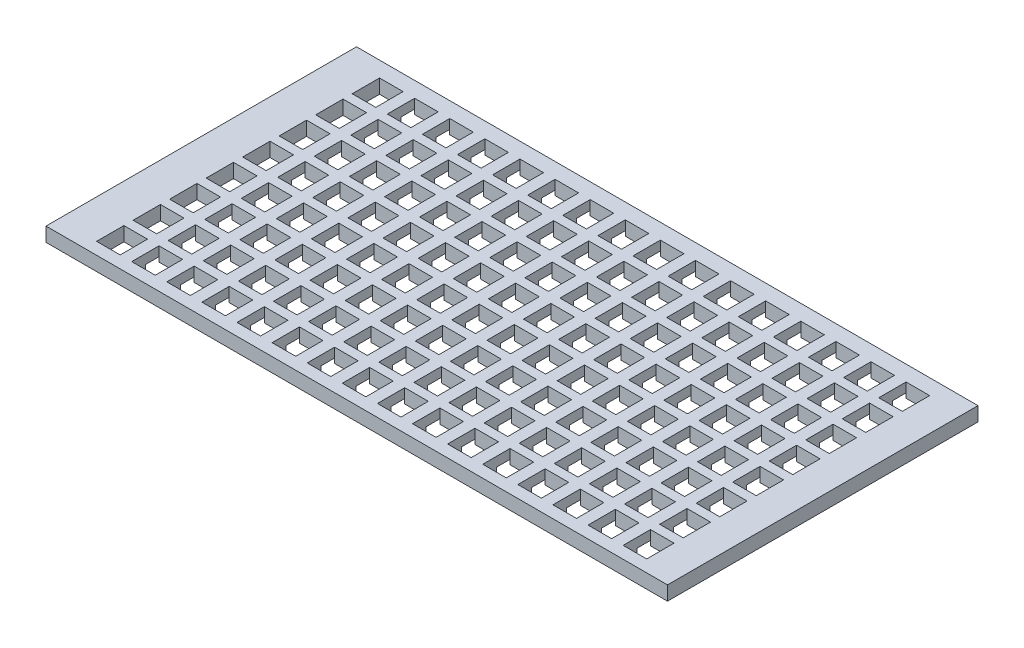
SolidWorks part; units mm, degrees
ref_plane "前视基准面" through (0, 0, 0) normal (0, 0, 1) x (1, 0, 0)
ref_plane "上视基准面" through (0, 0, 0) normal (0, 1, 0) x (1, 0, 0)
ref_plane "右视基准面" through (0, 0, 0) normal (1, 0, 0) x (0, 0, -1)
other "Configuration Table"
sketch "草图1" plane through (0, 0, 0) normal (0, 1, 0) x (1, 0, 0)
  line L1 (-65.95, 32.95) -> (65.95, 32.95)
  line L2 (-65.95, 32.95) -> (-65.95, -32.95)
  line L3 (-65.95, -32.95) -> (65.95, -32.95)
  line L4 (65.95, 32.95) -> (65.95, -32.95)
  line L5 (-65.95, 32.95) -> (65.95, -32.95) construction
  line L6 (-65.95, -32.95) -> (65.95, 32.95) construction
  point P0 (0, 0)
  dimension "D1" = 65.9
  dimension "D2" = 131.9
extrude "凸台-拉伸1" add sketch "草图1" along normal blind 3
sketch "草图2" plane through (0, 0, 0) normal (0, -1, 0) x (1, 0, 0)
  line L0 (-57.7744, 22.638) -> (-57.7744, 16.838)
  line L5 (-57.7744, 30.388) -> (-52.7744, 30.388)
  line L6 (-57.7744, 30.388) -> (-57.7744, 24.588)
  line L11 (-57.7744, 24.588) -> (-52.7744, 24.588)
  line L12 (-52.7744, 30.388) -> (-52.7744, 24.588)
  line L13 (-57.7744, 22.638) -> (-52.7744, 22.638)
  line L14 (-52.7744, 22.638) -> (-52.7744, 16.838)
  line L15 (-57.7744, 16.838) -> (-52.7744, 16.838)
  line L16 (-57.7744, 14.888) -> (-57.7744, 9.088)
  line L17 (-57.7744, 14.888) -> (-52.7744, 14.888)
  line L18 (-52.7744, 14.888) -> (-52.7744, 9.088)
  line L19 (-57.7744, 9.088) -> (-52.7744, 9.088)
  line L20 (-57.7744, 7.138) -> (-57.7744, 1.338)
  line L21 (-57.7744, 7.138) -> (-52.7744, 7.138)
  line L22 (-52.7744, 7.138) -> (-52.7744, 1.338)
  line L23 (-57.7744, 1.338) -> (-52.7744, 1.338)
  line L24 (-57.7744, -0.612) -> (-57.7744, -6.412)
  line L25 (-57.7744, -0.612) -> (-52.7744, -0.612)
  line L26 (-52.7744, -0.612) -> (-52.7744, -6.412)
  line L27 (-57.7744, -6.412) -> (-52.7744, -6.412)
  line L28 (-57.7744, -8.362) -> (-57.7744, -14.162)
  line L29 (-57.7744, -8.362) -> (-52.7744, -8.362)
  line L30 (-52.7744, -8.362) -> (-52.7744, -14.162)
  line L31 (-57.7744, -14.162) -> (-52.7744, -14.162)
  line L32 (-57.7744, -16.112) -> (-57.7744, -21.912)
  line L33 (-57.7744, -16.112) -> (-52.7744, -16.112)
  line L34 (-52.7744, -16.112) -> (-52.7744, -21.912)
  line L35 (-57.7744, -21.912) -> (-52.7744, -21.912)
  line L36 (-57.7744, -23.862) -> (-57.7744, -29.662)
  line L37 (-57.7744, -23.862) -> (-52.7744, -23.862)
  line L38 (-52.7744, -23.862) -> (-52.7744, -29.662)
  line L39 (-57.7744, -29.662) -> (-52.7744, -29.662)
  line L40 (-50.3244, 30.388) -> (-50.3244, 24.588)
  line L41 (-50.3244, 30.388) -> (-45.3244, 30.388)
  line L42 (-45.3244, 30.388) -> (-45.3244, 24.588)
  line L43 (-50.3244, 24.588) -> (-45.3244, 24.588)
  line L44 (-50.3244, 22.638) -> (-50.3244, 16.838)
  line L45 (-50.3244, 16.838) -> (-45.3244, 16.838)
  line L46 (-45.3244, 22.638) -> (-45.3244, 16.838)
  line L47 (-50.3244, 22.638) -> (-45.3244, 22.638)
  line L48 (-50.3244, 14.888) -> (-50.3244, 9.088)
  line L49 (-50.3244, 9.088) -> (-45.3244, 9.088)
  line L50 (-45.3244, 14.888) -> (-45.3244, 9.088)
  line L51 (-50.3244, 14.888) -> (-45.3244, 14.888)
  line L52 (-50.3244, 7.138) -> (-50.3244, 1.338)
  line L53 (-50.3244, 1.338) -> (-45.3244, 1.338)
  line L54 (-45.3244, 7.138) -> (-45.3244, 1.338)
  line L55 (-50.3244, 7.138) -> (-45.3244, 7.138)
  line L56 (-50.3244, -0.612) -> (-50.3244, -6.412)
  line L57 (-50.3244, -6.412) -> (-45.3244, -6.412)
  line L58 (-45.3244, -0.612) -> (-45.3244, -6.412)
  line L59 (-50.3244, -0.612) -> (-45.3244, -0.612)
  line L60 (-50.3244, -8.362) -> (-50.3244, -14.162)
  line L61 (-50.3244, -14.162) -> (-45.3244, -14.162)
  line L62 (-45.3244, -8.362) -> (-45.3244, -14.162)
  line L63 (-50.3244, -8.362) -> (-45.3244, -8.362)
  line L64 (-50.3244, -16.112) -> (-50.3244, -21.912)
  line L65 (-50.3244, -21.912) -> (-45.3244, -21.912)
  line L66 (-45.3244, -16.112) -> (-45.3244, -21.912)
  line L67 (-50.3244, -16.112) -> (-45.3244, -16.112)
  line L68 (-50.3244, -23.862) -> (-50.3244, -29.662)
  line L69 (-50.3244, -29.662) -> (-45.3244, -29.662)
  line L70 (-45.3244, -23.862) -> (-45.3244, -29.662)
  line L71 (-50.3244, -23.862) -> (-45.3244, -23.862)
  line L72 (-42.8744, 30.388) -> (-42.8744, 24.588)
  line L73 (-42.8744, 30.388) -> (-37.8744, 30.388)
  line L74 (-37.8744, 30.388) -> (-37.8744, 24.588)
  line L75 (-42.8744, 24.588) -> (-37.8744, 24.588)
  line L76 (-42.8744, 22.638) -> (-42.8744, 16.838)
  line L77 (-42.8744, 16.838) -> (-37.8744, 16.838)
  line L78 (-37.8744, 22.638) -> (-37.8744, 16.838)
  line L79 (-42.8744, 22.638) -> (-37.8744, 22.638)
  line L80 (-42.8744, 14.888) -> (-42.8744, 9.088)
  line L81 (-42.8744, 9.088) -> (-37.8744, 9.088)
  line L82 (-37.8744, 14.888) -> (-37.8744, 9.088)
  line L83 (-42.8744, 14.888) -> (-37.8744, 14.888)
  line L84 (-42.8744, 7.138) -> (-42.8744, 1.338)
  line L85 (-42.8744, 1.338) -> (-37.8744, 1.338)
  line L86 (-37.8744, 7.138) -> (-37.8744, 1.338)
  line L87 (-42.8744, 7.138) -> (-37.8744, 7.138)
  line L88 (-42.8744, -0.612) -> (-42.8744, -6.412)
  line L89 (-42.8744, -6.412) -> (-37.8744, -6.412)
  line L90 (-37.8744, -0.612) -> (-37.8744, -6.412)
  line L91 (-42.8744, -0.612) -> (-37.8744, -0.612)
  line L92 (-42.8744, -8.362) -> (-42.8744, -14.162)
  line L93 (-42.8744, -14.162) -> (-37.8744, -14.162)
  line L94 (-37.8744, -8.362) -> (-37.8744, -14.162)
  line L95 (-42.8744, -8.362) -> (-37.8744, -8.362)
  line L96 (-42.8744, -16.112) -> (-42.8744, -21.912)
  line L97 (-42.8744, -21.912) -> (-37.8744, -21.912)
  line L98 (-37.8744, -16.112) -> (-37.8744, -21.912)
  line L99 (-42.8744, -16.112) -> (-37.8744, -16.112)
  line L100 (-42.8744, -23.862) -> (-42.8744, -29.662)
  line L101 (-42.8744, -29.662) -> (-37.8744, -29.662)
  line L102 (-37.8744, -23.862) -> (-37.8744, -29.662)
  line L103 (-42.8744, -23.862) -> (-37.8744, -23.862)
  line L104 (-35.4244, 30.388) -> (-35.4244, 24.588)
  line L105 (-35.4244, 30.388) -> (-30.4244, 30.388)
  line L106 (-30.4244, 30.388) -> (-30.4244, 24.588)
  line L107 (-35.4244, 24.588) -> (-30.4244, 24.588)
  line L108 (-35.4244, 22.638) -> (-35.4244, 16.838)
  line L109 (-35.4244, 16.838) -> (-30.4244, 16.838)
  line L110 (-30.4244, 22.638) -> (-30.4244, 16.838)
  line L111 (-35.4244, 22.638) -> (-30.4244, 22.638)
  line L112 (-35.4244, 14.888) -> (-35.4244, 9.088)
  line L113 (-35.4244, 9.088) -> (-30.4244, 9.088)
  line L114 (-30.4244, 14.888) -> (-30.4244, 9.088)
  line L115 (-35.4244, 14.888) -> (-30.4244, 14.888)
  line L116 (-35.4244, 7.138) -> (-35.4244, 1.338)
  line L117 (-35.4244, 1.338) -> (-30.4244, 1.338)
  line L118 (-30.4244, 7.138) -> (-30.4244, 1.338)
  line L119 (-35.4244, 7.138) -> (-30.4244, 7.138)
  line L120 (-35.4244, -0.612) -> (-35.4244, -6.412)
  line L121 (-35.4244, -6.412) -> (-30.4244, -6.412)
  line L122 (-30.4244, -0.612) -> (-30.4244, -6.412)
  line L123 (-35.4244, -0.612) -> (-30.4244, -0.612)
  line L124 (-35.4244, -8.362) -> (-35.4244, -14.162)
  line L125 (-35.4244, -14.162) -> (-30.4244, -14.162)
  line L126 (-30.4244, -8.362) -> (-30.4244, -14.162)
  line L127 (-35.4244, -8.362) -> (-30.4244, -8.362)
  line L128 (-35.4244, -16.112) -> (-35.4244, -21.912)
  line L129 (-35.4244, -21.912) -> (-30.4244, -21.912)
  line L130 (-30.4244, -16.112) -> (-30.4244, -21.912)
  line L131 (-35.4244, -16.112) -> (-30.4244, -16.112)
  line L132 (-35.4244, -23.862) -> (-35.4244, -29.662)
  line L133 (-35.4244, -29.662) -> (-30.4244, -29.662)
  line L134 (-30.4244, -23.862) -> (-30.4244, -29.662)
  line L135 (-35.4244, -23.862) -> (-30.4244, -23.862)
  line L136 (-27.9744, 30.388) -> (-27.9744, 24.588)
  line L137 (-27.9744, 30.388) -> (-22.9744, 30.388)
  line L138 (-22.9744, 30.388) -> (-22.9744, 24.588)
  line L139 (-27.9744, 24.588) -> (-22.9744, 24.588)
  line L140 (-27.9744, 22.638) -> (-27.9744, 16.838)
  line L141 (-27.9744, 16.838) -> (-22.9744, 16.838)
  line L142 (-22.9744, 22.638) -> (-22.9744, 16.838)
  line L143 (-27.9744, 22.638) -> (-22.9744, 22.638)
  line L144 (-27.9744, 14.888) -> (-27.9744, 9.088)
  line L145 (-27.9744, 9.088) -> (-22.9744, 9.088)
  line L146 (-22.9744, 14.888) -> (-22.9744, 9.088)
  line L147 (-27.9744, 14.888) -> (-22.9744, 14.888)
  line L148 (-27.9744, 7.138) -> (-27.9744, 1.338)
  line L149 (-27.9744, 1.338) -> (-22.9744, 1.338)
  line L150 (-22.9744, 7.138) -> (-22.9744, 1.338)
  line L151 (-27.9744, 7.138) -> (-22.9744, 7.138)
  line L152 (-27.9744, -0.612) -> (-27.9744, -6.412)
  line L153 (-27.9744, -6.412) -> (-22.9744, -6.412)
  line L154 (-22.9744, -0.612) -> (-22.9744, -6.412)
  line L155 (-27.9744, -0.612) -> (-22.9744, -0.612)
  line L156 (-27.9744, -8.362) -> (-27.9744, -14.162)
  line L157 (-27.9744, -14.162) -> (-22.9744, -14.162)
  line L158 (-22.9744, -8.362) -> (-22.9744, -14.162)
  line L159 (-27.9744, -8.362) -> (-22.9744, -8.362)
  line L160 (-27.9744, -16.112) -> (-27.9744, -21.912)
  line L161 (-27.9744, -21.912) -> (-22.9744, -21.912)
  line L162 (-22.9744, -16.112) -> (-22.9744, -21.912)
  line L163 (-27.9744, -16.112) -> (-22.9744, -16.112)
  line L164 (-27.9744, -23.862) -> (-27.9744, -29.662)
  line L165 (-27.9744, -29.662) -> (-22.9744, -29.662)
  line L166 (-22.9744, -23.862) -> (-22.9744, -29.662)
  line L167 (-27.9744, -23.862) -> (-22.9744, -23.862)
  line L168 (-20.5244, 30.388) -> (-20.5244, 24.588)
  line L169 (-20.5244, 30.388) -> (-15.5244, 30.388)
  line L170 (-15.5244, 30.388) -> (-15.5244, 24.588)
  line L171 (-20.5244, 24.588) -> (-15.5244, 24.588)
  line L172 (-20.5244, 22.638) -> (-20.5244, 16.838)
  line L173 (-20.5244, 16.838) -> (-15.5244, 16.838)
  line L174 (-15.5244, 22.638) -> (-15.5244, 16.838)
  line L175 (-20.5244, 22.638) -> (-15.5244, 22.638)
  line L176 (-20.5244, 14.888) -> (-20.5244, 9.088)
  line L177 (-20.5244, 9.088) -> (-15.5244, 9.088)
  line L178 (-15.5244, 14.888) -> (-15.5244, 9.088)
  line L179 (-20.5244, 14.888) -> (-15.5244, 14.888)
  line L180 (-20.5244, 7.138) -> (-20.5244, 1.338)
  line L181 (-20.5244, 1.338) -> (-15.5244, 1.338)
  line L182 (-15.5244, 7.138) -> (-15.5244, 1.338)
  line L183 (-20.5244, 7.138) -> (-15.5244, 7.138)
  line L184 (-20.5244, -0.612) -> (-20.5244, -6.412)
  line L185 (-20.5244, -6.412) -> (-15.5244, -6.412)
  line L186 (-15.5244, -0.612) -> (-15.5244, -6.412)
  line L187 (-20.5244, -0.612) -> (-15.5244, -0.612)
  line L188 (-20.5244, -8.362) -> (-20.5244, -14.162)
  line L189 (-20.5244, -14.162) -> (-15.5244, -14.162)
  line L190 (-15.5244, -8.362) -> (-15.5244, -14.162)
  line L191 (-20.5244, -8.362) -> (-15.5244, -8.362)
  line L192 (-20.5244, -16.112) -> (-20.5244, -21.912)
  line L193 (-20.5244, -21.912) -> (-15.5244, -21.912)
  line L194 (-15.5244, -16.112) -> (-15.5244, -21.912)
  line L195 (-20.5244, -16.112) -> (-15.5244, -16.112)
  line L196 (-20.5244, -23.862) -> (-20.5244, -29.662)
  line L197 (-20.5244, -29.662) -> (-15.5244, -29.662)
  line L198 (-15.5244, -23.862) -> (-15.5244, -29.662)
  line L199 (-20.5244, -23.862) -> (-15.5244, -23.862)
  line L200 (-13.0744, 30.388) -> (-13.0744, 24.588)
  line L201 (-13.0744, 30.388) -> (-8.0744, 30.388)
  line L202 (-8.0744, 30.388) -> (-8.0744, 24.588)
  line L203 (-13.0744, 24.588) -> (-8.0744, 24.588)
  line L204 (-13.0744, 22.638) -> (-13.0744, 16.838)
  line L205 (-13.0744, 16.838) -> (-8.0744, 16.838)
  line L206 (-8.0744, 22.638) -> (-8.0744, 16.838)
  line L207 (-13.0744, 22.638) -> (-8.0744, 22.638)
  line L208 (-13.0744, 14.888) -> (-13.0744, 9.088)
  line L209 (-13.0744, 9.088) -> (-8.0744, 9.088)
  line L210 (-8.0744, 14.888) -> (-8.0744, 9.088)
  line L211 (-13.0744, 14.888) -> (-8.0744, 14.888)
  line L212 (-13.0744, 7.138) -> (-13.0744, 1.338)
  line L213 (-13.0744, 1.338) -> (-8.0744, 1.338)
  line L214 (-8.0744, 7.138) -> (-8.0744, 1.338)
  line L215 (-13.0744, 7.138) -> (-8.0744, 7.138)
  line L216 (-13.0744, -0.612) -> (-13.0744, -6.412)
  line L217 (-13.0744, -6.412) -> (-8.0744, -6.412)
  line L218 (-8.0744, -0.612) -> (-8.0744, -6.412)
  line L219 (-13.0744, -0.612) -> (-8.0744, -0.612)
  line L220 (-13.0744, -8.362) -> (-13.0744, -14.162)
  line L221 (-13.0744, -14.162) -> (-8.0744, -14.162)
  line L222 (-8.0744, -8.362) -> (-8.0744, -14.162)
  line L223 (-13.0744, -8.362) -> (-8.0744, -8.362)
  line L224 (-13.0744, -16.112) -> (-13.0744, -21.912)
  line L225 (-13.0744, -21.912) -> (-8.0744, -21.912)
  line L226 (-8.0744, -16.112) -> (-8.0744, -21.912)
  line L227 (-13.0744, -16.112) -> (-8.0744, -16.112)
  line L228 (-13.0744, -23.862) -> (-13.0744, -29.662)
  line L229 (-13.0744, -29.662) -> (-8.0744, -29.662)
  line L230 (-8.0744, -23.862) -> (-8.0744, -29.662)
  line L231 (-13.0744, -23.862) -> (-8.0744, -23.862)
  line L232 (-5.6244, 30.388) -> (-5.6244, 24.588)
  line L233 (-5.6244, 30.388) -> (-0.6244, 30.388)
  line L234 (-0.6244, 30.388) -> (-0.6244, 24.588)
  line L235 (-5.6244, 24.588) -> (-0.6244, 24.588)
  line L236 (-5.6244, 22.638) -> (-5.6244, 16.838)
  line L237 (-5.6244, 16.838) -> (-0.6244, 16.838)
  line L238 (-0.6244, 22.638) -> (-0.6244, 16.838)
  line L239 (-5.6244, 22.638) -> (-0.6244, 22.638)
  line L240 (-5.6244, 14.888) -> (-5.6244, 9.088)
  line L241 (-5.6244, 9.088) -> (-0.6244, 9.088)
  line L242 (-0.6244, 14.888) -> (-0.6244, 9.088)
  line L243 (-5.6244, 14.888) -> (-0.6244, 14.888)
  line L244 (-5.6244, 7.138) -> (-5.6244, 1.338)
  line L245 (-5.6244, 1.338) -> (-0.6244, 1.338)
  line L246 (-0.6244, 7.138) -> (-0.6244, 1.338)
  line L247 (-5.6244, 7.138) -> (-0.6244, 7.138)
  line L248 (-5.6244, -0.612) -> (-5.6244, -6.412)
  line L249 (-5.6244, -6.412) -> (-0.6244, -6.412)
  line L250 (-0.6244, -0.612) -> (-0.6244, -6.412)
  line L251 (-5.6244, -0.612) -> (-0.6244, -0.612)
  line L252 (-5.6244, -8.362) -> (-5.6244, -14.162)
  line L253 (-5.6244, -14.162) -> (-0.6244, -14.162)
  line L254 (-0.6244, -8.362) -> (-0.6244, -14.162)
  line L255 (-5.6244, -8.362) -> (-0.6244, -8.362)
  line L256 (-5.6244, -16.112) -> (-5.6244, -21.912)
  line L257 (-5.6244, -21.912) -> (-0.6244, -21.912)
  line L258 (-0.6244, -16.112) -> (-0.6244, -21.912)
  line L259 (-5.6244, -16.112) -> (-0.6244, -16.112)
  line L260 (-5.6244, -23.862) -> (-5.6244, -29.662)
  line L261 (-5.6244, -29.662) -> (-0.6244, -29.662)
  line L262 (-0.6244, -23.862) -> (-0.6244, -29.662)
  line L263 (-5.6244, -23.862) -> (-0.6244, -23.862)
  line L264 (1.8256, 30.388) -> (1.8256, 24.588)
  line L265 (1.8256, 30.388) -> (6.8256, 30.388)
  line L266 (6.8256, 30.388) -> (6.8256, 24.588)
  line L267 (1.8256, 24.588) -> (6.8256, 24.588)
  line L268 (1.8256, 22.638) -> (1.8256, 16.838)
  line L269 (1.8256, 16.838) -> (6.8256, 16.838)
  line L270 (6.8256, 22.638) -> (6.8256, 16.838)
  line L271 (1.8256, 22.638) -> (6.8256, 22.638)
  line L272 (1.8256, 14.888) -> (1.8256, 9.088)
  line L273 (1.8256, 9.088) -> (6.8256, 9.088)
  line L274 (6.8256, 14.888) -> (6.8256, 9.088)
  line L275 (1.8256, 14.888) -> (6.8256, 14.888)
  line L276 (1.8256, 7.138) -> (1.8256, 1.338)
  line L277 (1.8256, 1.338) -> (6.8256, 1.338)
  line L278 (6.8256, 7.138) -> (6.8256, 1.338)
  line L279 (1.8256, 7.138) -> (6.8256, 7.138)
  line L280 (1.8256, -0.612) -> (1.8256, -6.412)
  line L281 (1.8256, -6.412) -> (6.8256, -6.412)
  line L282 (6.8256, -0.612) -> (6.8256, -6.412)
  line L283 (1.8256, -0.612) -> (6.8256, -0.612)
  line L284 (1.8256, -8.362) -> (1.8256, -14.162)
  line L285 (1.8256, -14.162) -> (6.8256, -14.162)
  line L286 (6.8256, -8.362) -> (6.8256, -14.162)
  line L287 (1.8256, -8.362) -> (6.8256, -8.362)
  line L288 (1.8256, -16.112) -> (1.8256, -21.912)
  line L289 (1.8256, -21.912) -> (6.8256, -21.912)
  line L290 (6.8256, -16.112) -> (6.8256, -21.912)
  line L291 (1.8256, -16.112) -> (6.8256, -16.112)
  line L292 (1.8256, -23.862) -> (1.8256, -29.662)
  line L293 (1.8256, -29.662) -> (6.8256, -29.662)
  line L294 (6.8256, -23.862) -> (6.8256, -29.662)
  line L295 (1.8256, -23.862) -> (6.8256, -23.862)
  line L296 (9.2756, 30.388) -> (9.2756, 24.588)
  line L297 (9.2756, 30.388) -> (14.2756, 30.388)
  line L298 (14.2756, 30.388) -> (14.2756, 24.588)
  line L299 (9.2756, 24.588) -> (14.2756, 24.588)
  line L300 (9.2756, 22.638) -> (9.2756, 16.838)
  line L301 (9.2756, 16.838) -> (14.2756, 16.838)
  line L302 (14.2756, 22.638) -> (14.2756, 16.838)
  line L303 (9.2756, 22.638) -> (14.2756, 22.638)
  line L304 (9.2756, 14.888) -> (9.2756, 9.088)
  line L305 (9.2756, 9.088) -> (14.2756, 9.088)
  line L306 (14.2756, 14.888) -> (14.2756, 9.088)
  line L307 (9.2756, 14.888) -> (14.2756, 14.888)
  line L308 (9.2756, 7.138) -> (9.2756, 1.338)
  line L309 (9.2756, 1.338) -> (14.2756, 1.338)
  line L310 (14.2756, 7.138) -> (14.2756, 1.338)
  line L311 (9.2756, 7.138) -> (14.2756, 7.138)
  line L312 (9.2756, -0.612) -> (9.2756, -6.412)
  line L313 (9.2756, -6.412) -> (14.2756, -6.412)
  line L314 (14.2756, -0.612) -> (14.2756, -6.412)
  line L315 (9.2756, -0.612) -> (14.2756, -0.612)
  line L316 (9.2756, -8.362) -> (9.2756, -14.162)
  line L317 (9.2756, -14.162) -> (14.2756, -14.162)
  line L318 (14.2756, -8.362) -> (14.2756, -14.162)
  line L319 (9.2756, -8.362) -> (14.2756, -8.362)
  line L320 (9.2756, -16.112) -> (9.2756, -21.912)
  line L321 (9.2756, -21.912) -> (14.2756, -21.912)
  line L322 (14.2756, -16.112) -> (14.2756, -21.912)
  line L323 (9.2756, -16.112) -> (14.2756, -16.112)
  line L324 (9.2756, -23.862) -> (9.2756, -29.662)
  line L325 (9.2756, -29.662) -> (14.2756, -29.662)
  line L326 (14.2756, -23.862) -> (14.2756, -29.662)
  line L327 (9.2756, -23.862) -> (14.2756, -23.862)
  line L328 (16.7256, 30.388) -> (16.7256, 24.588)
  line L329 (16.7256, 30.388) -> (21.7256, 30.388)
  line L330 (21.7256, 30.388) -> (21.7256, 24.588)
  line L331 (16.7256, 24.588) -> (21.7256, 24.588)
  line L332 (16.7256, 22.638) -> (16.7256, 16.838)
  line L333 (16.7256, 16.838) -> (21.7256, 16.838)
  line L334 (21.7256, 22.638) -> (21.7256, 16.838)
  line L335 (16.7256, 22.638) -> (21.7256, 22.638)
  line L336 (16.7256, 14.888) -> (16.7256, 9.088)
  line L337 (16.7256, 9.088) -> (21.7256, 9.088)
  line L338 (21.7256, 14.888) -> (21.7256, 9.088)
  line L339 (16.7256, 14.888) -> (21.7256, 14.888)
  line L340 (16.7256, 7.138) -> (16.7256, 1.338)
  line L341 (16.7256, 1.338) -> (21.7256, 1.338)
  line L342 (21.7256, 7.138) -> (21.7256, 1.338)
  line L343 (16.7256, 7.138) -> (21.7256, 7.138)
  line L344 (16.7256, -0.612) -> (16.7256, -6.412)
  line L345 (16.7256, -6.412) -> (21.7256, -6.412)
  line L346 (21.7256, -0.612) -> (21.7256, -6.412)
  line L347 (16.7256, -0.612) -> (21.7256, -0.612)
  line L348 (16.7256, -8.362) -> (16.7256, -14.162)
  line L349 (16.7256, -14.162) -> (21.7256, -14.162)
  line L350 (21.7256, -8.362) -> (21.7256, -14.162)
  line L351 (16.7256, -8.362) -> (21.7256, -8.362)
  line L352 (16.7256, -16.112) -> (16.7256, -21.912)
  line L353 (16.7256, -21.912) -> (21.7256, -21.912)
  line L354 (21.7256, -16.112) -> (21.7256, -21.912)
  line L355 (16.7256, -16.112) -> (21.7256, -16.112)
  line L356 (16.7256, -23.862) -> (16.7256, -29.662)
  line L357 (16.7256, -29.662) -> (21.7256, -29.662)
  line L358 (21.7256, -23.862) -> (21.7256, -29.662)
  line L359 (16.7256, -23.862) -> (21.7256, -23.862)
  line L360 (24.1756, 30.388) -> (24.1756, 24.588)
  line L361 (24.1756, 30.388) -> (29.1756, 30.388)
  line L362 (29.1756, 30.388) -> (29.1756, 24.588)
  line L363 (24.1756, 24.588) -> (29.1756, 24.588)
  line L364 (24.1756, 22.638) -> (24.1756, 16.838)
  line L365 (24.1756, 16.838) -> (29.1756, 16.838)
  line L366 (29.1756, 22.638) -> (29.1756, 16.838)
  line L367 (24.1756, 22.638) -> (29.1756, 22.638)
  line L368 (24.1756, 14.888) -> (24.1756, 9.088)
  line L369 (24.1756, 9.088) -> (29.1756, 9.088)
  line L370 (29.1756, 14.888) -> (29.1756, 9.088)
  line L371 (24.1756, 14.888) -> (29.1756, 14.888)
  line L372 (24.1756, 7.138) -> (24.1756, 1.338)
  line L373 (24.1756, 1.338) -> (29.1756, 1.338)
  line L374 (29.1756, 7.138) -> (29.1756, 1.338)
  line L375 (24.1756, 7.138) -> (29.1756, 7.138)
  line L376 (24.1756, -0.612) -> (24.1756, -6.412)
  line L377 (24.1756, -6.412) -> (29.1756, -6.412)
  line L378 (29.1756, -0.612) -> (29.1756, -6.412)
  line L379 (24.1756, -0.612) -> (29.1756, -0.612)
  line L380 (24.1756, -8.362) -> (24.1756, -14.162)
  line L381 (24.1756, -14.162) -> (29.1756, -14.162)
  line L382 (29.1756, -8.362) -> (29.1756, -14.162)
  line L383 (24.1756, -8.362) -> (29.1756, -8.362)
  line L384 (24.1756, -16.112) -> (24.1756, -21.912)
  line L385 (24.1756, -21.912) -> (29.1756, -21.912)
  line L386 (29.1756, -16.112) -> (29.1756, -21.912)
  line L387 (24.1756, -16.112) -> (29.1756, -16.112)
  line L388 (24.1756, -23.862) -> (24.1756, -29.662)
  line L389 (24.1756, -29.662) -> (29.1756, -29.662)
  line L390 (29.1756, -23.862) -> (29.1756, -29.662)
  line L391 (24.1756, -23.862) -> (29.1756, -23.862)
  line L392 (31.6256, 30.388) -> (31.6256, 24.588)
  line L393 (31.6256, 30.388) -> (36.6256, 30.388)
  line L394 (36.6256, 30.388) -> (36.6256, 24.588)
  line L395 (31.6256, 24.588) -> (36.6256, 24.588)
  line L396 (31.6256, 22.638) -> (31.6256, 16.838)
  line L397 (31.6256, 16.838) -> (36.6256, 16.838)
  line L398 (36.6256, 22.638) -> (36.6256, 16.838)
  line L399 (31.6256, 22.638) -> (36.6256, 22.638)
  line L400 (31.6256, 14.888) -> (31.6256, 9.088)
  line L401 (31.6256, 9.088) -> (36.6256, 9.088)
  line L402 (36.6256, 14.888) -> (36.6256, 9.088)
  line L403 (31.6256, 14.888) -> (36.6256, 14.888)
  line L404 (31.6256, 7.138) -> (31.6256, 1.338)
  line L405 (31.6256, 1.338) -> (36.6256, 1.338)
  line L406 (36.6256, 7.138) -> (36.6256, 1.338)
  line L407 (31.6256, 7.138) -> (36.6256, 7.138)
  line L408 (31.6256, -0.612) -> (31.6256, -6.412)
  line L409 (31.6256, -6.412) -> (36.6256, -6.412)
  line L410 (36.6256, -0.612) -> (36.6256, -6.412)
  line L411 (31.6256, -0.612) -> (36.6256, -0.612)
  line L412 (31.6256, -8.362) -> (31.6256, -14.162)
  line L413 (31.6256, -14.162) -> (36.6256, -14.162)
  line L414 (36.6256, -8.362) -> (36.6256, -14.162)
  line L415 (31.6256, -8.362) -> (36.6256, -8.362)
  line L416 (31.6256, -16.112) -> (31.6256, -21.912)
  line L417 (31.6256, -21.912) -> (36.6256, -21.912)
  line L418 (36.6256, -16.112) -> (36.6256, -21.912)
  line L419 (31.6256, -16.112) -> (36.6256, -16.112)
  line L420 (31.6256, -23.862) -> (31.6256, -29.662)
  line L421 (31.6256, -29.662) -> (36.6256, -29.662)
  line L422 (36.6256, -23.862) -> (36.6256, -29.662)
  line L423 (31.6256, -23.862) -> (36.6256, -23.862)
  line L424 (39.0756, 30.388) -> (39.0756, 24.588)
  line L425 (39.0756, 30.388) -> (44.0756, 30.388)
  line L426 (44.0756, 30.388) -> (44.0756, 24.588)
  line L427 (39.0756, 24.588) -> (44.0756, 24.588)
  line L428 (39.0756, 22.638) -> (39.0756, 16.838)
  line L429 (39.0756, 16.838) -> (44.0756, 16.838)
  line L430 (44.0756, 22.638) -> (44.0756, 16.838)
  line L431 (39.0756, 22.638) -> (44.0756, 22.638)
  line L432 (39.0756, 14.888) -> (39.0756, 9.088)
  line L433 (39.0756, 9.088) -> (44.0756, 9.088)
  line L434 (44.0756, 14.888) -> (44.0756, 9.088)
  line L435 (39.0756, 14.888) -> (44.0756, 14.888)
  line L436 (39.0756, 7.138) -> (39.0756, 1.338)
  line L437 (39.0756, 1.338) -> (44.0756, 1.338)
  line L438 (44.0756, 7.138) -> (44.0756, 1.338)
  line L439 (39.0756, 7.138) -> (44.0756, 7.138)
  line L440 (39.0756, -0.612) -> (39.0756, -6.412)
  line L441 (39.0756, -6.412) -> (44.0756, -6.412)
  line L442 (44.0756, -0.612) -> (44.0756, -6.412)
  line L443 (39.0756, -0.612) -> (44.0756, -0.612)
  line L444 (39.0756, -8.362) -> (39.0756, -14.162)
  line L445 (39.0756, -14.162) -> (44.0756, -14.162)
  line L446 (44.0756, -8.362) -> (44.0756, -14.162)
  line L447 (39.0756, -8.362) -> (44.0756, -8.362)
  line L448 (39.0756, -16.112) -> (39.0756, -21.912)
  line L449 (39.0756, -21.912) -> (44.0756, -21.912)
  line L450 (44.0756, -16.112) -> (44.0756, -21.912)
  line L451 (39.0756, -16.112) -> (44.0756, -16.112)
  line L452 (39.0756, -23.862) -> (39.0756, -29.662)
  line L453 (39.0756, -29.662) -> (44.0756, -29.662)
  line L454 (44.0756, -23.862) -> (44.0756, -29.662)
  line L455 (39.0756, -23.862) -> (44.0756, -23.862)
  line L456 (46.5256, 30.388) -> (46.5256, 24.588)
  line L457 (46.5256, 30.388) -> (51.5256, 30.388)
  line L458 (51.5256, 30.388) -> (51.5256, 24.588)
  line L459 (46.5256, 24.588) -> (51.5256, 24.588)
  line L460 (46.5256, 22.638) -> (46.5256, 16.838)
  line L461 (46.5256, 16.838) -> (51.5256, 16.838)
  line L462 (51.5256, 22.638) -> (51.5256, 16.838)
  line L463 (46.5256, 22.638) -> (51.5256, 22.638)
  line L464 (46.5256, 14.888) -> (46.5256, 9.088)
  line L465 (46.5256, 9.088) -> (51.5256, 9.088)
  line L466 (51.5256, 14.888) -> (51.5256, 9.088)
  line L467 (46.5256, 14.888) -> (51.5256, 14.888)
  line L468 (46.5256, 7.138) -> (46.5256, 1.338)
  line L469 (46.5256, 1.338) -> (51.5256, 1.338)
  line L470 (51.5256, 7.138) -> (51.5256, 1.338)
  line L471 (46.5256, 7.138) -> (51.5256, 7.138)
  line L472 (46.5256, -0.612) -> (46.5256, -6.412)
  line L473 (46.5256, -6.412) -> (51.5256, -6.412)
  line L474 (51.5256, -0.612) -> (51.5256, -6.412)
  line L475 (46.5256, -0.612) -> (51.5256, -0.612)
  line L476 (46.5256, -8.362) -> (46.5256, -14.162)
  line L477 (46.5256, -14.162) -> (51.5256, -14.162)
  line L478 (51.5256, -8.362) -> (51.5256, -14.162)
  line L479 (46.5256, -8.362) -> (51.5256, -8.362)
  line L480 (46.5256, -16.112) -> (46.5256, -21.912)
  line L481 (46.5256, -21.912) -> (51.5256, -21.912)
  line L482 (51.5256, -16.112) -> (51.5256, -21.912)
  line L483 (46.5256, -16.112) -> (51.5256, -16.112)
  line L484 (46.5256, -23.862) -> (46.5256, -29.662)
  line L485 (46.5256, -29.662) -> (51.5256, -29.662)
  line L486 (51.5256, -23.862) -> (51.5256, -29.662)
  line L487 (46.5256, -23.862) -> (51.5256, -23.862)
  line L488 (53.9756, 30.388) -> (53.9756, 24.588)
  line L489 (53.9756, 30.388) -> (58.9756, 30.388)
  line L490 (58.9756, 30.388) -> (58.9756, 24.588)
  line L491 (53.9756, 24.588) -> (58.9756, 24.588)
  line L492 (53.9756, 22.638) -> (53.9756, 16.838)
  line L493 (53.9756, 16.838) -> (58.9756, 16.838)
  line L494 (58.9756, 22.638) -> (58.9756, 16.838)
  line L495 (53.9756, 22.638) -> (58.9756, 22.638)
  line L496 (53.9756, 14.888) -> (53.9756, 9.088)
  line L497 (53.9756, 9.088) -> (58.9756, 9.088)
  line L498 (58.9756, 14.888) -> (58.9756, 9.088)
  line L499 (53.9756, 14.888) -> (58.9756, 14.888)
  line L500 (53.9756, 7.138) -> (53.9756, 1.338)
  line L501 (53.9756, 1.338) -> (58.9756, 1.338)
  line L502 (58.9756, 7.138) -> (58.9756, 1.338)
  line L503 (53.9756, 7.138) -> (58.9756, 7.138)
  line L504 (53.9756, -0.612) -> (53.9756, -6.412)
  line L505 (53.9756, -6.412) -> (58.9756, -6.412)
  line L506 (58.9756, -0.612) -> (58.9756, -6.412)
  line L507 (53.9756, -0.612) -> (58.9756, -0.612)
  line L508 (53.9756, -8.362) -> (53.9756, -14.162)
  line L509 (53.9756, -14.162) -> (58.9756, -14.162)
  line L510 (58.9756, -8.362) -> (58.9756, -14.162)
  line L511 (53.9756, -8.362) -> (58.9756, -8.362)
  line L512 (53.9756, -16.112) -> (53.9756, -21.912)
  line L513 (53.9756, -21.912) -> (58.9756, -21.912)
  line L514 (58.9756, -16.112) -> (58.9756, -21.912)
  line L515 (53.9756, -16.112) -> (58.9756, -16.112)
  line L516 (53.9756, -23.862) -> (53.9756, -29.662)
  line L517 (53.9756, -29.662) -> (58.9756, -29.662)
  line L518 (58.9756, -23.862) -> (58.9756, -29.662)
  line L519 (53.9756, -23.862) -> (58.9756, -23.862)
  point P0 (0, 0)
  dimension "D1" = 2.45
  dimension "D2" = 1.95
  dimension "D3" = 5
  dimension "D4" = 5.8
  dimension "D5" = 8
  dimension "D6" = 16
extrude "切除-拉伸2" cut sketch "草图2" against normal through all
sketch "草图3" plane through (0, 0, 0) normal (0, -1, 0) x (1, 0, 0)
  line L0 (58.9756, 24.588) -> (58.9756, 30.388) construction
  line L513 (58.9756, 27.488) -> (61.4256, 27.488)
  line L514 (58.9756, 27.488) -> (58.9756, 23.488)
  line L515 (58.9756, 23.488) -> (61.4256, 23.488)
  line L516 (61.4256, 27.488) -> (61.4256, 23.488)
  dimension "D4" = 4
  dimension "D3" = 2.45
extrude "切除-拉伸3" cut sketch "草图3" against normal blind 1
pattern_linear "阵列(线性)1" count 16 spacing 7.45 along (-1, 0, 0) count 8 spacing 7.75 along (0, 0, -1) of "切除-拉伸3"
